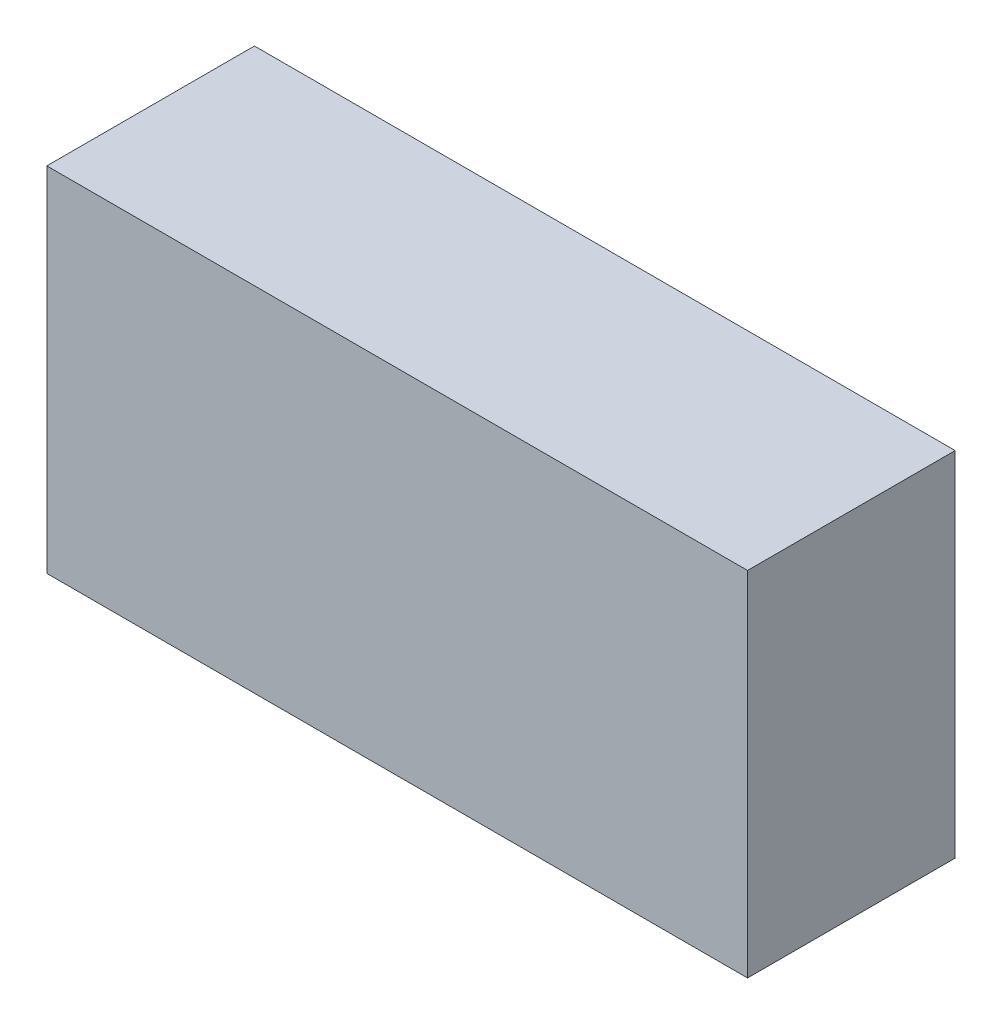
SolidWorks part; units mm, degrees
ref_plane "Спереди" through (0, 0, 0) normal (0, 0, 1) x (1, 0, 0)
ref_plane "Сверху" through (0, 0, 0) normal (0, 1, 0) x (1, 0, 0)
ref_plane "Справа" through (0, 0, 0) normal (1, 0, 0) x (0, 0, -1)
other "Configuration Table"
sketch "Эскиз1" plane through (0, 0, 0) normal (0, 1, 0) x (1, 0, 0)
  line L1 (0, 0) -> (135, 0)
  line L2 (0, 0) -> (0, 40)
  line L3 (0, 40) -> (135, 40)
  line L4 (135, 0) -> (135, 40)
  line L5 (67.5, 40) -> (67.5, 0) construction
  line L6 (0, 20) -> (135, 20) construction
  point P232 (67.5, 20)
  dimension "D1" = 135
  dimension "D2" = 40
extrude "Корпус" add sketch "Эскиз1" along normal blind 68
sketch "Эскиз2" plane through (0, 0, 0) normal (0, -1, 0) x (1, 0, 0)
  line L0 (0, -40) -> (0, 0) construction
  line L1 (2, -3) -> (41, -3)
  line L2 (2, -3) -> (2, -18)
  line L3 (2, -18) -> (41, -18)
  line L4 (41, -3) -> (41, -18)
  line L5 (21.5, -18) -> (21.5, -3) construction
  line L6 (2, -10.5) -> (41, -10.5) construction
  line L7 (48, -3) -> (87, -3)
  line L8 (48, -3) -> (48, -18)
  line L9 (48, -18) -> (87, -18)
  line L10 (87, -3) -> (87, -18)
  line L11 (67.5, -18) -> (67.5, -3) construction
  line L12 (48, -10.5) -> (87, -10.5) construction
  line L13 (94, -3) -> (133, -3)
  line L14 (94, -3) -> (94, -18)
  line L15 (94, -18) -> (133, -18)
  line L16 (133, -3) -> (133, -18)
  line L17 (113.5, -18) -> (113.5, -3) construction
  line L18 (94, -10.5) -> (133, -10.5) construction
  line L19 (48, -21) -> (87, -21)
  line L20 (48, -21) -> (48, -36)
  line L21 (48, -36) -> (87, -36)
  line L22 (87, -21) -> (87, -36)
  line L23 (67.5, -36) -> (67.5, -21) construction
  line L24 (48, -28.5) -> (87, -28.5) construction
  line L25 (94, -21) -> (133, -21)
  line L26 (94, -21) -> (94, -36)
  line L27 (94, -36) -> (133, -36)
  line L28 (133, -21) -> (133, -36)
  line L29 (113.5, -36) -> (113.5, -21) construction
  line L30 (94, -28.5) -> (133, -28.5) construction
  line L31 (2, -21) -> (41, -21)
  line L32 (2, -21) -> (2, -36)
  line L33 (2, -36) -> (41, -36)
  line L34 (41, -21) -> (41, -36)
  line L35 (21.5, -36) -> (21.5, -21) construction
  line L36 (2, -28.5) -> (41, -28.5) construction
  line L37 (135, 0) -> (135, -40) construction
  line L38 (0, 0) -> (135, 0) construction
  point P16 (67.5, -10.5)
  point P25 (113.5, -10.5)
  point P34 (67.5, -28.5)
  point P43 (113.5, -28.5)
  point P52 (21.5, -28.5)
  point P292 (21.5, -10.5)
  dimension "D1" = 2
  dimension "D2" = 39
  dimension "D3" = 15
  dimension "D6" = 2
  dimension "D7" = 3
  dimension "D4" = 3
  dimension "D5" = 2
extrude "Вырез-Вытянуть1" cut sketch "Эскиз2" against normal blind 66
sketch "Эскиз4" plane through (0, 0, 0) normal (0, -1, 0) x (1, 0, 0)
  line L0 (41, -18) -> (41, -3) construction
  line L1 (41, -5.7894) -> (94, -5.7894)
  line L2 (41, -5.7894) -> (41, -15.2176)
  line L3 (41, -15.2176) -> (94, -15.2176)
  line L4 (94, -5.7894) -> (94, -15.2176)
  line L5 (67.5, -15.2176) -> (67.5, -5.7894) construction
  line L6 (41, -10.5035) -> (94, -10.5035) construction
  line L7 (94, -3) -> (94, -18) construction
  point P776 (67.5, -10.5035)
extrude "Вырез-Вытянуть2" cut sketch "Эскиз4" against normal blind 66
ref_plane "Плоскость1" through (41, 0, -21) normal (0, 0, 1) x (1, 0, 0)
sketch "Эскиз6" plane through (0, 0, 0) normal (0, -1, 0) x (1, 0, 0)
  line L0 (41, -36) -> (41, -21) construction
  line L1 (41, -23.2117) -> (94, -23.2117)
  line L2 (41, -23.2117) -> (41, -33.3649)
  line L3 (41, -33.3649) -> (94, -33.3649)
  line L4 (94, -23.2117) -> (94, -33.3649)
  line L5 (67.5, -33.3649) -> (67.5, -23.2117) construction
  line L6 (41, -28.2883) -> (94, -28.2883) construction
  line L7 (94, -21) -> (94, -36) construction
  point P348 (67.5, -28.2883)
extrude "Вырез-Вытянуть3" cut sketch "Эскиз6" against normal blind 66
sketch "Эскиз7" plane through (0, 0, 0) normal (0, -1, 0) x (1, 0, 0)
  line L0 (2, -18) -> (41, -18) construction
  line L1 (7.6517, -18) -> (37.9858, -18)
  line L2 (7.6517, -18) -> (7.6517, -21)
  line L3 (7.6517, -21) -> (37.9858, -21)
  line L4 (37.9858, -18) -> (37.9858, -21)
  line L5 (22.8187, -21) -> (22.8187, -18) construction
  line L6 (7.6517, -19.5) -> (37.9858, -19.5) construction
  line L7 (41, -21) -> (2, -21) construction
  line L8 (48, -18) -> (87, -18) construction
  line L9 (50.2834, -18) -> (84.0334, -18)
  line L10 (50.2834, -18) -> (50.2834, -21)
  line L11 (50.2834, -21) -> (84.0334, -21)
  line L12 (84.0334, -18) -> (84.0334, -21)
  line L13 (67.1584, -21) -> (67.1584, -18) construction
  line L14 (50.2834, -19.5) -> (84.0334, -19.5) construction
  line L15 (87, -21) -> (48, -21) construction
  line L16 (94, -18) -> (133, -18) construction
  line L17 (96.6043, -18) -> (127.6216, -18)
  line L18 (96.6043, -18) -> (96.6043, -21)
  line L19 (96.6043, -21) -> (127.6216, -21)
  line L20 (127.6216, -18) -> (127.6216, -21)
  line L21 (112.1129, -21) -> (112.1129, -18) construction
  line L22 (96.6043, -19.5) -> (127.6216, -19.5) construction
  line L23 (133, -21) -> (94, -21) construction
  point P168 (22.8187, -19.5)
  point P249 (67.1584, -19.5)
  point P282 (112.1129, -19.5)
extrude "Вырез-Вытянуть4" cut sketch "Эскиз7" against normal blind 66
sketch "Эскиз8" plane through (41, 0, -21) normal (0, 0, 1) x (1, 0, 0)
sketch "Эскиз9" plane through (0, 0, 0) normal (0, -1, 0) x (1, 0, 0)
